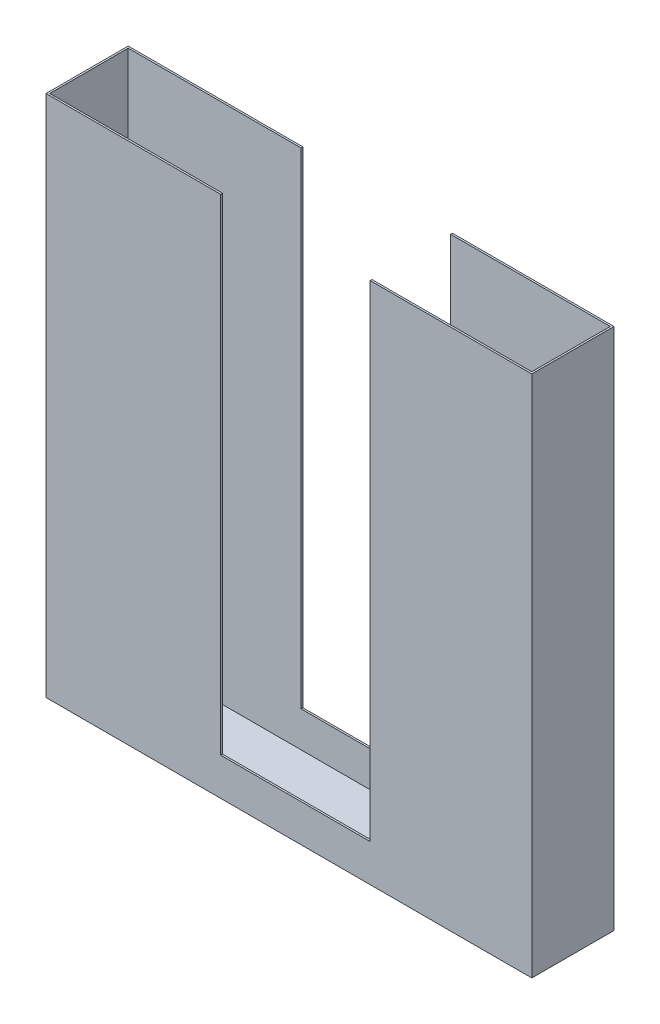
SolidWorks part; units mm, degrees
ref_plane "Front Plane" through (0, 0, 0) normal (0, 0, 1) x (1, 0, 0)
ref_plane "Top Plane" through (0, 0, 0) normal (0, 1, 0) x (1, 0, 0)
ref_plane "Right Plane" through (0, 0, 0) normal (1, 0, 0) x (0, 0, -1)
sketch "Sketch2" plane through (0, 0, 0) normal (0, 0, 1) x (1, 0, 0)
  line L1 (-118.5559, 36.2254) -> (294.1941, 36.2254)
  line L2 (-118.5559, 36.2254) -> (-118.5559, -408.2746)
  line L3 (-118.5559, -408.2746) -> (294.1941, -408.2746)
  line L4 (294.1941, 36.2254) -> (294.1941, -408.2746)
  dimension "D1" = 412.75
  dimension "D2" = 444.5
extrude "Boss-Extrude1" add sketch "Sketch2" along normal blind 69.85 contours L1 L4 L3 L2
shell "Shell1" thickness 1.5875
sketch "Sketch4" plane through (0, 0, 69.85) normal (0, 0, 1) x (1, 0, 0)
  line L1 (29.9024, 36.2499) -> (156.9024, 36.2499)
  line L2 (29.9024, 36.2499) -> (29.9024, -376.5001)
  line L3 (29.9024, -376.5001) -> (156.9024, -376.5001)
  line L4 (156.9024, 36.2499) -> (156.9024, -376.5001)
  dimension "D1" = 127
  dimension "D2" = 412.75
extrude "Cut-Extrude1" cut sketch "Sketch4" against normal blind 69.85
